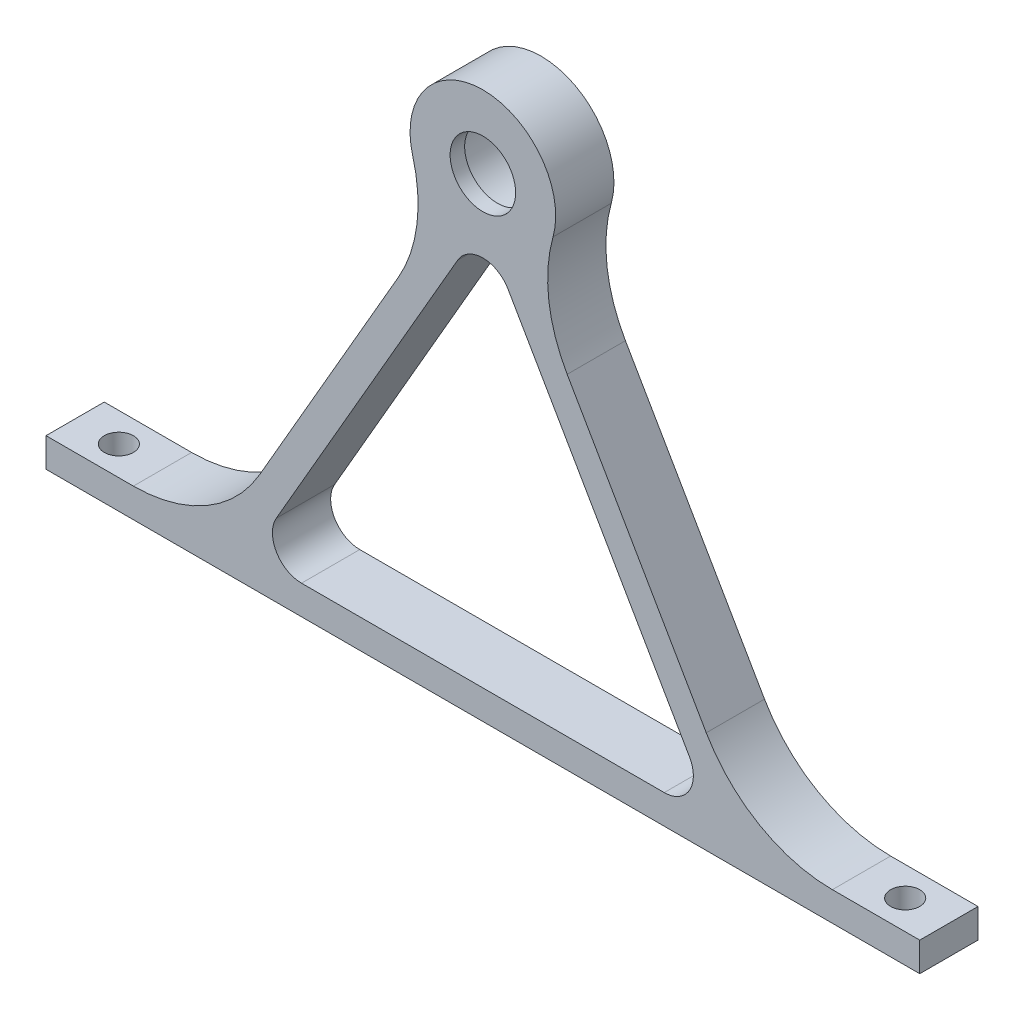
SolidWorks part; units mm, degrees
ref_plane "Plan de face" through (0, 0, 0) normal (0, 0, 1) x (1, 0, 0)
ref_plane "Plan de dessus" through (0, 0, 0) normal (0, 1, 0) x (1, 0, 0)
ref_plane "Plan de droite" through (0, 0, 0) normal (1, 0, 0) x (0, 0, -1)
sketch "Esquisse1" plane through (0, 0, 0) normal (0, 0, 1) x (1, 0, 0)
  line L0 (0, 0) -> (0, 59.8294) construction
  line L1 (0, 0) -> (42.4268, 0) construction
  line L2 (-30, 0) -> (30, 0)
  line L3 (-30, 0) -> (-30, 2)
  line L4 (30, 0) -> (30, 2)
  line L5 (-30, 2) -> (-24, 2)
  line L6 (-15.3397, 7) -> (-5.7891, 23.5422)
  line L7 (5.7891, 23.5422) -> (15.3397, 7)
  line L8 (24, 2) -> (30, 2)
  line L9 (-12.453, 2) -> (12.453, 2)
  line L10 (14.185, 5) -> (1.7321, 26.5692)
  line L11 (-1.7321, 26.5692) -> (-14.185, 5)
  arc A0 (-4.8164, 31.2269) -> (4.8164, 31.2269) centre (0, 32.5692) cw
  arc A1 (24, 2) -> (15.3397, 7) centre (24, 12) cw
  arc A2 (-15.3397, 7) -> (-24, 2) centre (-24, 12) cw
  arc A3 (5.7891, 23.5422) -> (4.8164, 31.2269) centre (14.4493, 28.5422) cw
  arc A4 (-5.7891, 23.5422) -> (-4.8164, 31.2269) centre (-14.4493, 28.5422) ccw
  arc A5 (12.453, 2) -> (14.185, 5) centre (12.453, 4) ccw
  arc A6 (-12.453, 2) -> (-14.185, 5) centre (-12.453, 4) cw
  arc A7 (-1.7321, 26.5692) -> (1.7321, 26.5692) centre (0, 25.5692) cw
  arc A8 (4.8164, 31.2269) -> (0, 27.5692) centre (0, 32.5692) cw construction
  circle A10 centre (0, 32.5692) radius 3
  point P9 (0, 27.5692)
  point P19 (18.2265, 2)
  point P22 (-18.2265, 2)
  point P25 (2.9205, 28.5108)
  point P28 (-2.9205, 28.5108)
  point P31 (15.9171, 2)
  point P34 (-15.9171, 2)
  point P35 (0, 0)
  point P36 (0, 0)
  dimension "D3" = 10
  dimension "D7" = 5
  dimension "D8" = 6
  dimension "D10" = 2
  dimension "D11" = 10
  dimension "D1" = 60
  dimension "D2" = 2
  dimension "D4" = 6
  dimension "D5" = 60
  dimension "D9" = 2
extrude "Boss.-Extru.2" add sketch "Esquisse1" along normal blind 4 contours A3 A0 A4 L6 A2 L5 L3 L2 L4 L8 A1 L7 | A10 | L11 A6 L9 A5 L10 A7
sketch "Esquisse2" plane through (0, 0, 4) normal (0, 0, 1) x (1, 0, 0)
  circle A0 centre (0, 32.5692) radius 5
  circle A1 centre (0, 32.5692) radius 2.25
  arc A2 (4.8164, 31.2269) -> (-4.8164, 31.2269) centre (0, 32.5692) ccw construction
  circle A3 centre (0, 32.5692) radius 3 construction
  point P4 (0, 0)
  dimension "D1" = 0.75
extrude "Boss.-Extru.3" add sketch "Esquisse2" against normal blind 1 contours A0 | A1
sketch "Esquisse3" plane through (0, 2, 0) normal (0, 1, 0) x (1, 0, 0)
  line L0 (30, -2) -> (24, -2) construction
  line L1 (30, -4) -> (30, 0) construction
  line L2 (24, -4) -> (24, 0) construction
  line L3 (0, 0) -> (0, -4) construction
  line L4 (-5, -4) -> (5, -4) construction
  circle A0 centre (27, -2) radius 1
  circle A1 centre (-27, -2) radius 1
  dimension "D1" = 2
extrude "Enlèv. mat.-Extru.2" cut sketch "Esquisse3" against normal through all both and the other way through all
